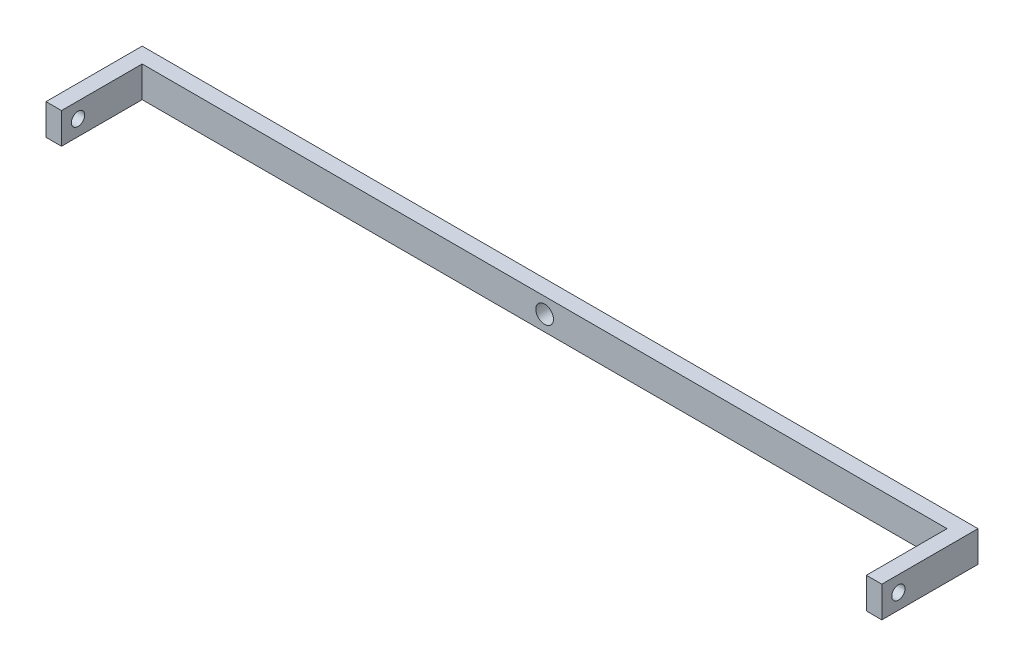
SolidWorks part; units mm, degrees
material "Acrylic (Medium-high impact)"
ref_plane "Front Plane" through (0, 0, 0) normal (0, 0, 1) x (1, 0, 0)
ref_plane "Top Plane" through (0, 0, 0) normal (0, 1, 0) x (1, 0, 0)
ref_plane "Right Plane" through (0, 0, 0) normal (1, 0, 0) x (0, 0, -1)
sketch "Sketch1" plane through (0, 0, 0) normal (0, 1, 0) x (1, 0, 0)
  line L0 (92.75, 0) -> (-92.75, 0) construction
  line L1 (-92.75, 0) -> (-92.75, -20) construction
  line L2 (92.75, 0) -> (92.75, -20) construction
  line L3 (94.5, 1.75) -> (94.5, -20)
  line L4 (94.5, 1.75) -> (-94.5, 1.75)
  line L5 (-94.5, 1.75) -> (-94.5, -20)
  line L6 (91, -1.75) -> (91, -20)
  line L7 (91, -1.75) -> (-91, -1.75)
  line L8 (-91, -1.75) -> (-91, -20)
  line L9 (-94.5, -20) -> (-91, -20)
  line L10 (91, -20) -> (94.5, -20)
  point P4 (0, 0)
  dimension "D1" = 185.5
  dimension "D2" = 20
  dimension "D3" = 1.75
  dimension "D4" = 1.75
extrude "Boss-Extrude1" add sketch "Sketch1" along normal mid plane 7
sketch "Sketch3" plane through (0, 0, -1.75) normal (0, 0, -1) x (-1, 0, 0)
  circle A0 centre (0, 0) radius 2
  dimension "D1" = 4
extrude "Cut-Extrude1" cut sketch "Sketch3" against normal blind 7
sketch "Sketch4" plane through (-94.5, 0, 0) normal (-1, 0, 0) x (0, 0, 1)
  line L0 (-1.75, 3.5) -> (-1.75, -3.5) construction
  circle A0 centre (16.25, 0) radius 1.5
  dimension "D2" = 3
  dimension "D1" = 18
extrude "Cut-Extrude2" cut sketch "Sketch4" against normal through all both and the other way through all
